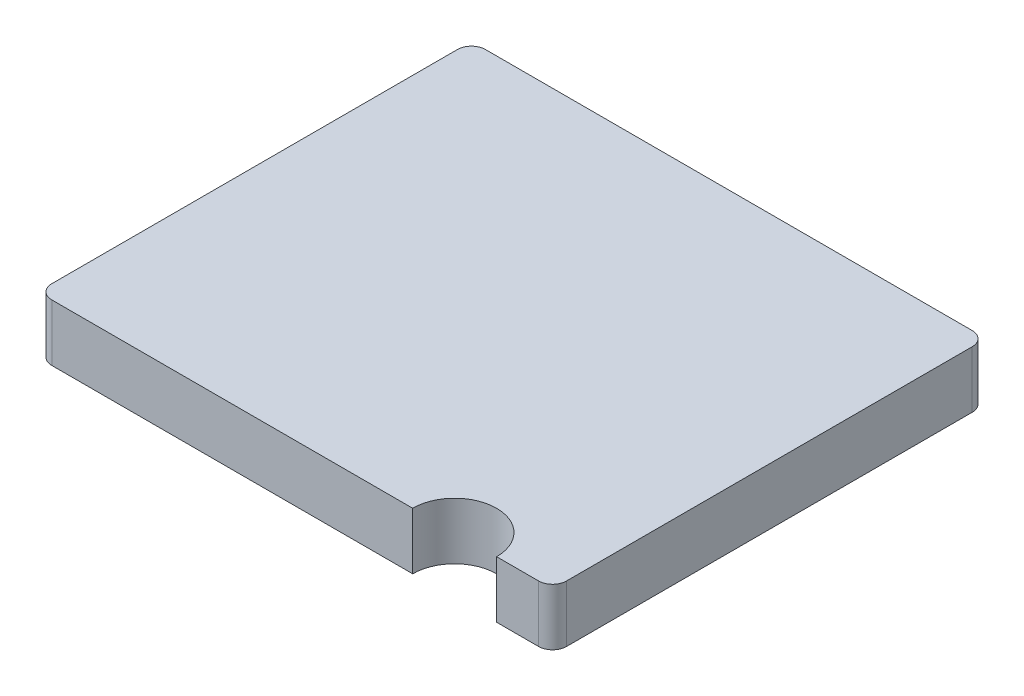
SolidWorks part; units mm, degrees
material "1060-H18"
ref_plane "Front Plane" through (0, 0, 0) normal (0, 0, 1) x (1, 0, 0)
ref_plane "Top Plane" through (0, 0, 0) normal (0, 1, 0) x (1, 0, 0)
ref_plane "Right Plane" through (0, 0, 0) normal (1, 0, 0) x (0, 0, -1)
sketch "Sketch1" plane through (0, 0, 0) normal (0, 1, 0) x (1, 0, 0)
  line L1 (-0.92, 0.775) -> (0.92, 0.775)
  line L2 (-0.92, 0.775) -> (-0.92, -0.775)
  line L3 (-0.92, -0.775) -> (0.92, -0.775)
  line L4 (0.92, 0.775) -> (0.92, -0.775)
  line L5 (-0.92, 0.775) -> (0.92, -0.775) construction
  line L6 (-0.92, -0.775) -> (0.92, 0.775) construction
  point P0 (0, 0)
  dimension "D1" = 1.84
  dimension "D2" = 1.55
extrude "Boss-Extrude1" add sketch "Sketch1" along normal blind 0.203
fillet "Fillet1" radius 0.05 4 edges at (-0.92, 0.1015, -0.775) (0.92, 0.1015, -0.775) (0.92, 0.1015, 0.775) (-0.92, 0.1015, 0.775)
sketch "Sketch2" plane through (0, 0.203, 0) normal (0, 1, 0) x (1, 0, 0)
  line L0 (-0.87, -0.775) -> (0.87, -0.775) construction
  line L1 (0.92, -0.725) -> (0.92, 0.725) construction
  circle A0 centre (0.57, -0.775) radius 0.15
  dimension "D1" = 0.3
  dimension "D2" = 0.35
extrude "Cut-Extrude1" cut sketch "Sketch2" against normal through all
